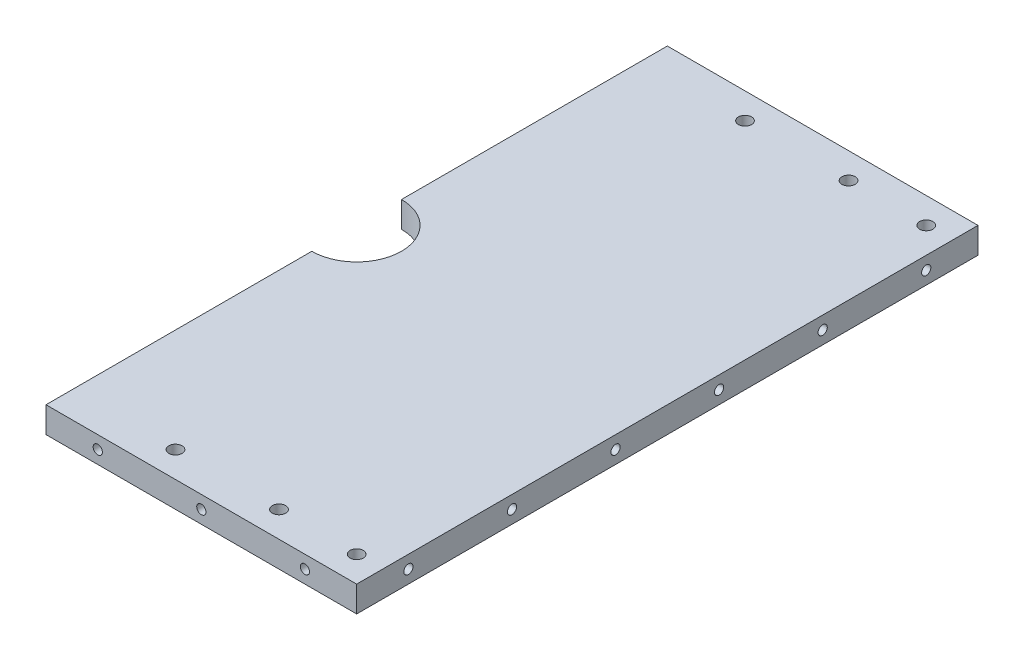
SolidWorks part; units mm, degrees
material "Copper"
ref_plane "Front Plane" through (0, 0, 0) normal (0, 0, 1) x (1, 0, 0)
ref_plane "Top Plane" through (0, 0, 0) normal (0, 1, 0) x (1, 0, 0)
ref_plane "Right Plane" through (0, 0, 0) normal (1, 0, 0) x (0, 0, -1)
sketch "Sketch1" plane through (0, 0, 0) normal (0, 1, 0) x (1, 0, 0)
  line L0 (0, -11) -> (0, -76.2)
  line L1 (0, 76.2) -> (76.2, 76.2)
  line L2 (0, 76.2) -> (0, 11)
  line L3 (0, -76.2) -> (76.2, -76.2)
  line L4 (76.2, 76.2) -> (76.2, -76.2)
  line L5 (0, 0) -> (76.2, 0) construction
  arc A0 (0, -11) -> (0, 11) centre (0, 0) ccw
  circle A1 centre (69.85, 69.85) radius 1.6319
  circle A2 centre (69.85, -69.85) radius 1.6319
  circle A3 centre (50.8, 69.85) radius 1.6319
  circle A4 centre (25.4, 69.85) radius 1.6319
  circle A5 centre (50.8, -69.85) radius 1.6319
  circle A6 centre (25.4, -69.85) radius 1.6319
  dimension "D1" = 11
  dimension "D4" = 3.2639
  dimension "D2" = 76.2
  dimension "D3" = 152.4
  dimension "D5" = 6.35
  dimension "D6" = 6.35
  dimension "D7" = 25.4
  dimension "D8" = 19.05
extrude "Boss-Extrude1" add sketch "Sketch1" along normal blind 6.35
hole_wizard "#4-40 Tapped Hole1" positions "3DSketch1" profile "Sketch2" tap size "#4-40" standard "ANSI Inch"
sketch3d "3DSketch1"
  line L0 (76.2, 6.35, 76.2) -> (76.2, 6.35, -76.2) construction
  line L2 (76.2, 6.35, 76.2) -> (76.2, 0, 76.2) construction
  point P0 (76.2, 3.175, 63.5)
  dimension "D1" = 3.175
  dimension "D2" = 12.7
sketch "Sketch2" plane through (76.2, 3.175, 63.5) normal (0, 1, 0) x (0, 0, -1)
  line L0 (0, 0) -> (0, 8.2792)
  line L1 (0, 8.2792) -> (1.1303, 7.6)
  line L2 (1.1303, 7.6) -> (1.1303, 0)
  line L5 (1.1303, 0) -> (0, 0)
  line L10 (0, 8.2792) -> (-1.1303, 7.6) construction
  line L11 (0, -6.35) -> (0, 107.95) construction
  dimension "Tap Drill Dia." = 2.2606
  dimension "Tap Drill Depth" = 7.6
  dimension "Drill Angle" = 118
cosmetic thread "Hole Thread1" parameters "D1"=5.69, "D2"=2.8448
pattern_linear "LPattern1" count 6 spacing 25.4 along (0, 0, -1) of "#4-40 Tapped Hole1"
cosmetic thread "Hole Thread2" parameters "D1"=5.69, "D2"=2.8448
cosmetic thread "Hole Thread3" parameters "D1"=5.69, "D2"=2.8448
cosmetic thread "Hole Thread4" parameters "D1"=5.69, "D2"=2.8448
cosmetic thread "Hole Thread5" parameters "D1"=5.69, "D2"=2.8448
cosmetic thread "Hole Thread6" parameters "D1"=5.69, "D2"=2.8448
hole_wizard "#4-40 Tapped Hole2" positions "3DSketch2" profile "Sketch3" tap size "#4-40" standard "ANSI Inch"
sketch3d "3DSketch2"
  line L0 (0, 6.35, 76.2) -> (76.2, 6.35, 76.2) construction
  line L1 (76.2, 6.35, 76.2) -> (76.2, 0, 76.2) construction
  point P0 (63.5, 3.175, 76.2)
  dimension "D1" = 3.175
  dimension "D2" = 12.7
sketch "Sketch3" plane through (63.5, 3.175, 76.2) normal (1, 0, 0) x (0, -1, 0)
  line L0 (0, 0) -> (0, 8.2792)
  line L1 (0, 8.2792) -> (1.1303, 7.6)
  line L2 (1.1303, 7.6) -> (1.1303, 0)
  line L5 (1.1303, 0) -> (0, 0)
  line L10 (0, 8.2792) -> (-1.1303, 7.6) construction
  line L11 (0, -6.35) -> (0, 107.95) construction
  dimension "Tap Drill Dia." = 2.2606
  dimension "Tap Drill Depth" = 7.6
  dimension "Drill Angle" = 118
cosmetic thread "Hole Thread7" parameters "D1"=5.69, "D2"=2.8448
pattern_linear "LPattern2" count 3 spacing 25.4 along (-1, 0, 0) of "#4-40 Tapped Hole2"
cosmetic thread "Hole Thread8" parameters "D1"=5.69, "D2"=2.8448
cosmetic thread "Hole Thread9" parameters "D1"=5.69, "D2"=2.8448
ref_plane "Plane1" through (0, 0, 0) normal (0, 0, 1) x (1, 0, 0)
mirror "Mirror1" about plane through (0, 0, 0) normal (0, 0, 1) of "LPattern2", "#4-40 Tapped Hole2"
cosmetic thread "Hole Thread10" parameters "D1"=5.69, "D2"=2.8448
cosmetic thread "Hole Thread11" parameters "D1"=5.69, "D2"=2.8448
cosmetic thread "Hole Thread12" parameters "D1"=5.69, "D2"=2.8448
equation "\"D6@Sketch1\"=\"D5@Sketch1\""
